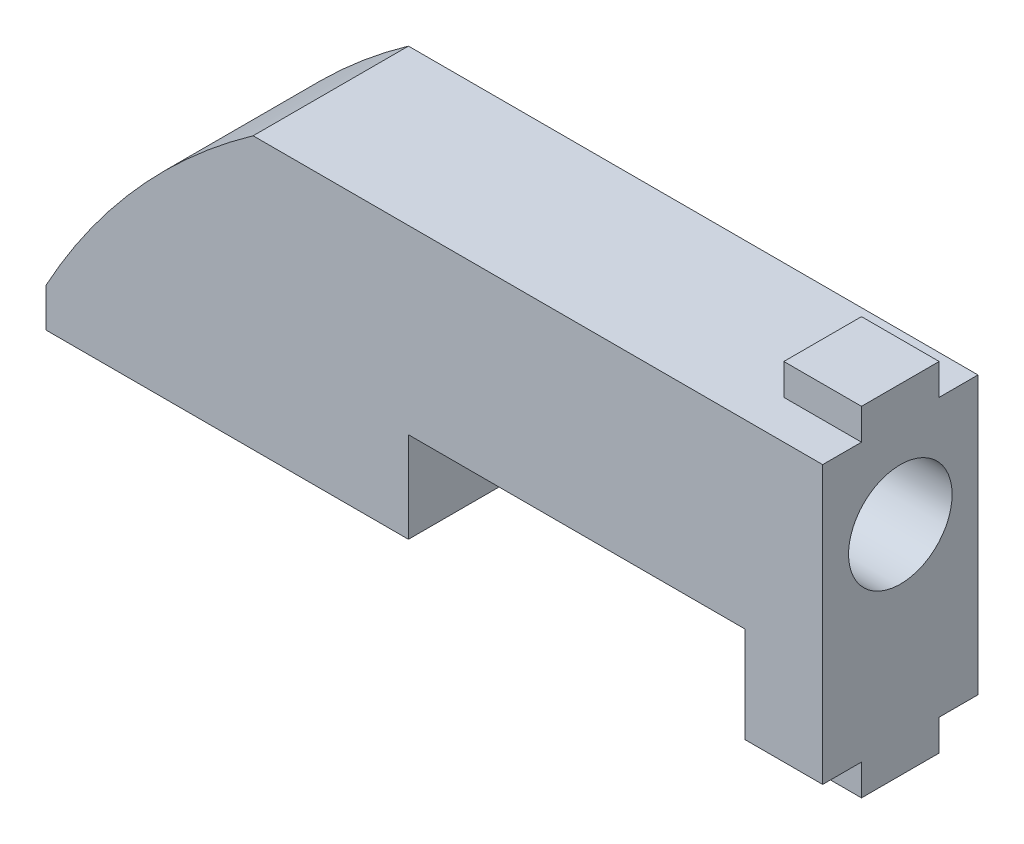
SolidWorks part; units mm, degrees
material "Alliage 7079"
ref_plane "Face" through (0, 0, 0) normal (0, 0, 1) x (1, 0, 0)
ref_plane "Dessus" through (0, 0, 0) normal (0, 1, 0) x (1, 0, 0)
ref_plane "Droite" through (0, 0, 0) normal (1, 0, 0) x (0, 0, -1)
sketch "Esquisse1" plane through (0, 0, 0) normal (0, 0, 1) x (1, 0, 0)
  line L0 (0, 0) -> (0, 1.5)
  line L2 (8, 10.5) -> (30, 10.5)
  line L3 (30, 10.5) -> (30, -0.2)
  line L4 (27, -0.2) -> (27, 3.5)
  line L5 (27, 3.5) -> (14, 3.5)
  line L6 (14, 3.5) -> (14, 0)
  line L7 (14, 0) -> (0, 0)
  line L9 (27, -0.2) -> (30, -0.2)
  arc A0 (8, 10.5) -> (0, 1.5) centre (23.3666, -11.2147) ccw
  dimension "D6" = 26.6019
  dimension "D1" = 10.7
  dimension "D2" = 10.5
  dimension "D3" = 1.5
  dimension "D4" = 13
  dimension "D5" = 7
  dimension "D7" = 22
  dimension "D8" = 8
  dimension "D9" = 14
extrude "Extrusion1" add sketch "Esquisse1" along normal mid plane 6
sketch "Esquisse2" plane through (0, 10.5, 0) normal (0, 1, 0) x (1, 0, 0)
  line L0 (30, -3) -> (30, 3) construction
  line L1 (30, 1.5) -> (27, 1.5)
  line L2 (30, 1.5) -> (30, -1.5)
  line L3 (30, -1.5) -> (27, -1.5)
  line L4 (27, 1.5) -> (27, -1.5)
  line L5 (31.5625, 0) -> (23.3666, 0) construction
  line L6 (23.3666, -3) -> (23.3666, 3) construction
  line L7 (30, 3) -> (8, 3) construction
  dimension "D1" = 3
  dimension "D2" = 3
  dimension "D3" = 3
extrude "Extrusion2" add sketch "Esquisse2" along normal blind 1.2
sketch "Esquisse3" plane through (0, -0.2, 0) normal (0, -1, 0) x (1, 0, 0)
  line L0 (27, 3) -> (27, -3) construction
  line L1 (27, 1.5) -> (30, 1.5)
  line L2 (27, 1.5) -> (27, -1.5)
  line L3 (27, -1.5) -> (30, -1.5)
  line L4 (30, 1.5) -> (30, -1.5)
  line L5 (30.8829, 0) -> (25.166, 0) construction
  line L6 (14, 3) -> (27, 3) construction
  line L7 (30, 3) -> (30, -3) construction
  dimension "D1" = 3
  dimension "D2" = 3
extrude "Extrusion3" add sketch "Esquisse3" along normal blind 1.2
hole_wizard "Diamètre du perçage Ø4.0 (4)1" positions "Esquisse5" profile "Esquisse4" hole size "Ø4.0" standard "ISO"
sketch "Esquisse5" plane through (30, 0, 0) normal (1, 0, 0) x (0, 0, -1)
  line L0 (-3, -0.2) -> (-3, 10.5) construction
  line L2 (1.5, -0.2) -> (3, -0.2) construction
  line L3 (1.5, 10.5) -> (3, 10.5) construction
  point P0 (0, 7)
  point P7 (2.25, -0.2)
  point P10 (2.25, 10.5)
  dimension "D1" = 3
  dimension "D2" = 7.2
  dimension "D3" = 3.5
sketch "Esquisse4" plane through (30, 7, 0) normal (0, 1, 0) x (0, 0, -1)
  line L0 (0, 0) -> (0, 4.2017)
  line L1 (0, 4.2017) -> (2, 3)
  line L2 (2, 3) -> (2, 0)
  line L5 (2, 0) -> (0, 0)
  line L10 (0, 4.2017) -> (-2, 3) construction
  line L11 (0, -6.35) -> (0, 107.95) construction
  dimension "Diamètre du perçage" = 4
  dimension "Profondeur du perçage" = 3
  dimension "Angle de pointe" = 118
